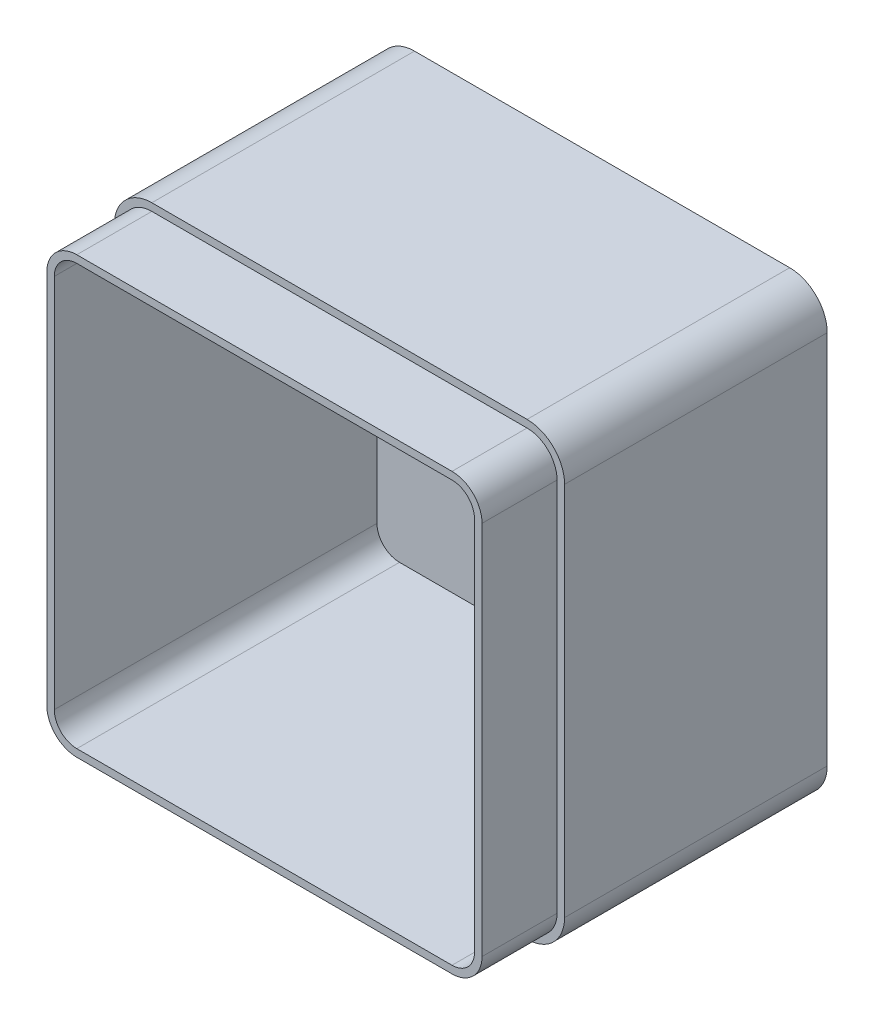
SolidWorks part; units mm, degrees
ref_plane "Front Plane" through (0, 0, 0) normal (0, 0, 1) x (1, 0, 0)
ref_plane "Top Plane" through (0, 0, 0) normal (0, 1, 0) x (1, 0, 0)
ref_plane "Right Plane" through (0, 0, 0) normal (1, 0, 0) x (0, 0, -1)
sketch "Sketch1" plane through (0, 0, 0) normal (0, 0, 1) x (1, 0, 0)
  line L1 (0, 0) -> (120, 0)
  line L2 (0, 0) -> (0, 120)
  line L3 (0, 120) -> (120, 120)
  line L4 (120, 0) -> (120, 120)
  dimension "D1" = 120
  dimension "D2" = 120
extrude "Boss-Extrude2" add sketch "Sketch1" along normal blind 90
fillet "Fillet1" radius 10 4 edges at (120, 0, 45) (0, 0, 45) (0, 120, 45) (120, 120, 45)
shell "Shell1" thickness 4
sketch "Sketch2" plane through (0, 0, 90) normal (0, 0, 1) x (1, 0, 0)
  line L8 (10, 2) -> (110, 2)
  line L9 (118, 10) -> (118, 110)
  line L10 (110, 118) -> (10, 118)
  line L11 (2, 110) -> (2, 10)
  line L12 (10, 2) -> (110, 2)
  line L13 (118, 10) -> (118, 110)
  line L14 (110, 118) -> (10, 118)
  line L15 (2, 110) -> (2, 10)
  arc A8 (110, 2) -> (118, 10) centre (110, 10) ccw
  arc A9 (118, 110) -> (110, 118) centre (110, 110) ccw
  arc A10 (10, 118) -> (2, 110) centre (10, 110) ccw
  arc A11 (2, 10) -> (10, 2) centre (10, 10) ccw
  arc A12 (110, 2) -> (118, 10) centre (110, 10) ccw
  arc A13 (118, 110) -> (110, 118) centre (110, 110) ccw
  arc A14 (10, 118) -> (2, 110) centre (10, 110) ccw
  arc A15 (2, 10) -> (10, 2) centre (10, 10) ccw
  dimension "D1" = 2
extrude "Cut-Extrude1" cut sketch "Sketch2" against normal blind 20 flip side to cut
